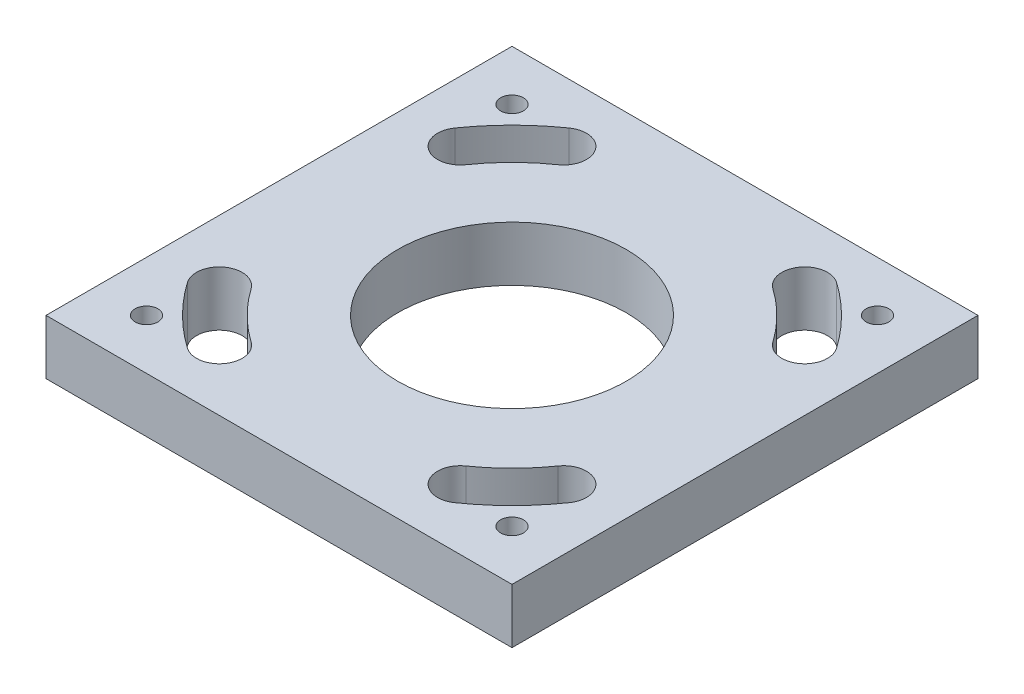
SolidWorks part; units mm, degrees
ref_plane "Face" through (0, 0, 0) normal (0, 0, 1) x (1, 0, 0)
ref_plane "Dessus" through (0, 0, 0) normal (0, 1, 0) x (1, 0, 0)
ref_plane "Droite" through (0, 0, 0) normal (1, 0, 0) x (0, 0, -1)
sketch "Esquisse1" plane through (0, 0, 0) normal (0, 1, 0) x (1, 0, 0)
  line L0 (-59.8186, 41.8854) -> (0, 0) construction
  line L1 (-80.9625, -80.9625) -> (80.9625, -80.9625)
  line L2 (-80.9625, -80.9625) -> (-80.9625, 80.9625)
  line L3 (-80.9625, 80.9625) -> (80.9625, 80.9625)
  line L4 (80.9625, -80.9625) -> (80.9625, 80.9625)
  line L5 (-80.9625, -80.9625) -> (80.9625, 80.9625) construction
  line L6 (-80.9625, 80.9625) -> (80.9625, -80.9625) construction
  line L7 (0, 0) -> (-41.8854, 59.8186) construction
  circle A0 centre (0, 0) radius 39.6875
  arc A1 (-41.8854, 59.8186) -> (-59.8186, 41.8854) centre (0, 0) ccw construction
  arc A2 (-46.4382, 66.3206) -> (-66.3206, 46.4382) centre (0, 0) ccw
  arc A3 (-37.3327, 53.3166) -> (-53.3166, 37.3327) centre (0, 0) ccw
  arc A4 (-37.3327, 53.3166) -> (-46.4382, 66.3206) centre (-41.8854, 59.8186) ccw
  arc A5 (-66.3206, 46.4382) -> (-53.3166, 37.3327) centre (-59.8186, 41.8854) ccw
  arc A6 (59.8186, 41.8854) -> (41.8854, 59.8186) centre (0, 0) ccw construction
  arc A7 (66.3206, 46.4382) -> (46.4382, 66.3206) centre (0, 0) ccw
  arc A8 (53.3166, 37.3327) -> (37.3327, 53.3166) centre (0, 0) ccw
  arc A9 (53.3166, 37.3327) -> (66.3206, 46.4382) centre (59.8186, 41.8854) ccw
  arc A10 (46.4382, 66.3206) -> (37.3327, 53.3166) centre (41.8854, 59.8186) ccw
  arc A11 (41.8854, -59.8186) -> (59.8186, -41.8854) centre (0, 0) ccw construction
  arc A12 (46.4382, -66.3206) -> (66.3206, -46.4382) centre (0, 0) ccw
  arc A13 (37.3327, -53.3166) -> (53.3166, -37.3327) centre (0, 0) ccw
  arc A14 (37.3327, -53.3166) -> (46.4382, -66.3206) centre (41.8854, -59.8186) ccw
  arc A15 (66.3206, -46.4382) -> (53.3166, -37.3327) centre (59.8186, -41.8854) ccw
  arc A16 (-59.8186, -41.8854) -> (-41.8854, -59.8186) centre (0, 0) ccw construction
  arc A17 (-66.3206, -46.4382) -> (-46.4382, -66.3206) centre (0, 0) ccw
  arc A18 (-53.3166, -37.3327) -> (-37.3327, -53.3166) centre (0, 0) ccw
  arc A19 (-53.3166, -37.3327) -> (-66.3206, -46.4382) centre (-59.8186, -41.8854) ccw
  arc A20 (-46.4382, -66.3206) -> (-37.3327, -53.3166) centre (-41.8854, -59.8186) ccw
  point P0 (0, 0)
  point P10 (-51.6365, 51.6365)
  point P23 (51.6365, 51.6365)
  point P30 (51.6365, -51.6365)
  point P37 (-51.6365, -51.6365)
  point P42 (0, 0)
  dimension "D3" = 79.375
  dimension "D6" = 7.9375
  dimension "D1" = 161.925
  dimension "D2" = 161.925
  dimension "D4" = 73.025
  dimension "D5" = 20
  dimension "D7" = 4
extrude "Boss.-Extru.1" add sketch "Esquisse1" against normal blind 19.05
hole_wizard "Trou taraudé 3/8-161" positions "Esquisse2" profile "Esquisse3" tap size "3/8-16" standard "Ansi Inch" end condition through all
sketch "Esquisse2" plane through (0, 0, 0) normal (0, 1, 0) x (1, 0, 0)
  line L0 (80.9625, 80.9625) -> (-80.9625, 80.9625) construction
  line L1 (-80.9625, 80.9625) -> (-80.9625, -80.9625) construction
  point P0 (-63.5, 63.5)
  point P2 (63.5, 63.5)
  point P5 (-63.5, -63.5)
  point P7 (63.5, -63.5)
  point P14 (0, 0)
  point P15 (0, 0)
  point P16 (0, 0)
  dimension "D1" = 127
  dimension "D2" = 127
  dimension "D3" = 17.4625
  dimension "D4" = 17.4625
sketch "Esquisse3" plane through (-63.5, 0, -63.5) normal (1, 0, 0) x (0, 0, 1)
  line L0 (0, 0) -> (0, 19.05)
  line L1 (0, 19.05) -> (3.9687, 19.05)
  line L2 (3.9687, 19.05) -> (3.9687, 0)
  line L5 (3.9687, 0) -> (0, 0)
  line L11 (0, -6.35) -> (0, 107.95) construction
  dimension "Diamètre du trou pour taraudage jusqu'au prochain" = 7.9375
  dimension "Profondeur du trou pour taraudage jusqu'au prochain" = 19.05
cosmetic thread "Filetage de perçage1" parameters "D2"=9.525
cosmetic thread "Filetage de perçage2" parameters "D2"=9.525
cosmetic thread "Filetage de perçage3" parameters "D2"=9.525
cosmetic thread "Filetage de perçage4" parameters "D2"=9.525
